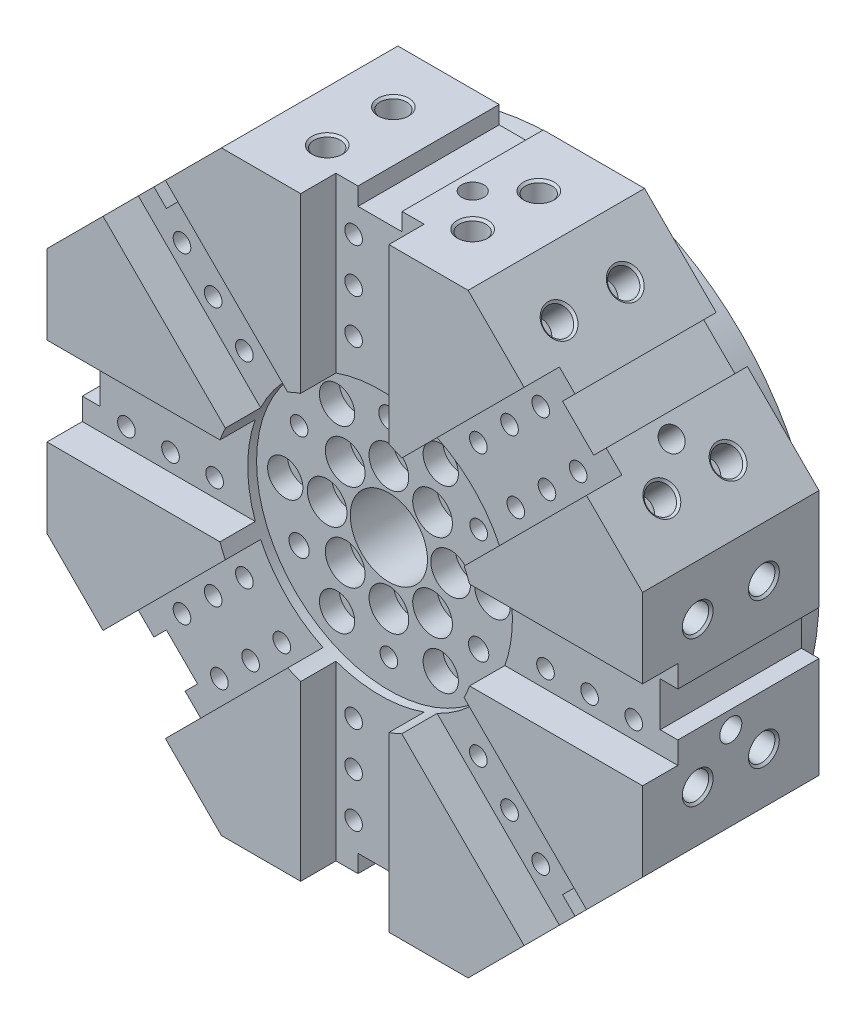
SolidWorks part; units mm, degrees
ref_plane "前视基准面" through (0, 0, 0) normal (0, 0, 1) x (1, 0, 0)
ref_plane "上视基准面" through (0, 0, 0) normal (0, 1, 0) x (1, 0, 0)
ref_plane "右视基准面" through (0, 0, 0) normal (1, 0, 0) x (0, 0, -1)
sketch "草图7" plane through (0, 0, 0) normal (0, 0, 1) x (1, 0, 0)
  line L1 (55.9188, 135) -> (-55.9188, 135)
  line L2 (-55.9188, 135) -> (-135, 55.9188)
  line L3 (-135, 55.9188) -> (-135, -55.9188)
  line L4 (-135, -55.9188) -> (-55.9188, -135)
  line L5 (-55.9188, -135) -> (55.9188, -135)
  line L6 (55.9188, -135) -> (135, -55.9188)
  line L7 (135, -55.9188) -> (135, 55.9188)
  line L8 (135, 55.9188) -> (55.9188, 135)
  circle A0 centre (0, 0) radius 135 construction
  dimension "D1" = 270
extrude "凸台-拉伸3" add sketch "草图7" along normal blind 80
sketch "草图8" plane through (0, 0, 80) normal (0, 0, 1) x (1, 0, 0)
  circle A0 centre (0, 0) radius 60
  dimension "D1" = 120
extrude "切除-拉伸3" cut sketch "草图8" against normal blind 20
sketch "草图9" plane through (0, 0, 80) normal (0, 0, 1) x (1, 0, 0)
  line L0 (0, 0) -> (228.1259, 0) construction
  line L1 (135, -55.9188) -> (135, 55.9188) construction
  line L2 (135, -20) -> (135, 20)
  line L3 (56.5685, -20) -> (135, -20)
  line L4 (56.5685, 20) -> (135, 20)
  line L5 (81.3173, -109.6016) -> (109.6016, -81.3173)
  line L6 (0, 20) -> (228.1259, 20) construction
  line L7 (0, -20) -> (228.1259, -20) construction
  line L8 (25.8579, -54.1421) -> (81.3173, -109.6016)
  line L9 (54.1421, -25.8579) -> (109.6016, -81.3173)
  line L10 (0, 0) -> (161.3093, -161.3093) construction
  line L11 (-20, -135) -> (20, -135)
  line L12 (-20, -56.5685) -> (-20, -135)
  line L13 (20, -56.5685) -> (20, -135)
  line L14 (0, 0) -> (0, -228.1259) construction
  line L15 (-109.6016, -81.3173) -> (-81.3173, -109.6016)
  line L16 (-54.1421, -25.8579) -> (-109.6016, -81.3173)
  line L17 (-25.8579, -54.1421) -> (-81.3173, -109.6016)
  line L18 (0, 0) -> (-161.3093, -161.3093) construction
  line L19 (-135, 20) -> (-135, -20)
  line L20 (-56.5685, 20) -> (-135, 20)
  line L21 (-56.5685, -20) -> (-135, -20)
  line L22 (0, 0) -> (-228.1259, 0) construction
  line L23 (-81.3173, 109.6016) -> (-109.6016, 81.3173)
  line L24 (-25.8579, 54.1421) -> (-81.3173, 109.6016)
  line L25 (-54.1421, 25.8579) -> (-109.6016, 81.3173)
  line L26 (0, 0) -> (-161.3093, 161.3093) construction
  line L27 (20, 135) -> (-20, 135)
  line L28 (20, 56.5685) -> (20, 135)
  line L29 (-20, 56.5685) -> (-20, 135)
  line L30 (0, 0) -> (0, 228.1259) construction
  line L31 (109.6016, 81.3173) -> (81.3173, 109.6016)
  line L32 (54.1421, 25.8579) -> (109.6016, 81.3173)
  line L33 (25.8579, 54.1421) -> (81.3173, 109.6016)
  line L34 (0, 0) -> (161.3093, 161.3093) construction
  circle A0 centre (0, 0) radius 60 construction
  arc A1 (56.5685, -20) -> (56.5685, 20) centre (0, 0) ccw
  arc A2 (25.8579, -54.1421) -> (54.1421, -25.8579) centre (0, 0) ccw
  arc A3 (-20, -56.5685) -> (20, -56.5685) centre (0, 0) ccw
  arc A4 (-54.1421, -25.8579) -> (-25.8579, -54.1421) centre (0, 0) ccw
  arc A5 (-56.5685, 20) -> (-56.5685, -20) centre (0, 0) ccw
  arc A6 (-25.8579, 54.1421) -> (-54.1421, 25.8579) centre (0, 0) ccw
  arc A7 (20, 56.5685) -> (-20, 56.5685) centre (0, 0) ccw
  arc A8 (54.1421, 25.8579) -> (25.8579, 54.1421) centre (0, 0) ccw
  dimension "D1" = 20
  dimension "D2" = 20
extrude "切除-拉伸4" cut sketch "草图9" against normal blind 16
sketch "草图10" plane through (0, 0, 64) normal (0, 0, 1) x (1, 0, 0)
  line L0 (0, 0) -> (184.1219, 0) construction
  line L1 (135, -20) -> (135, 20) construction
  line L2 (135, 10) -> (127, 10)
  line L3 (135, 10) -> (135, -10)
  line L4 (135, -10) -> (127, -10)
  line L5 (127, 10) -> (127, -10)
  dimension "D1" = 20
  dimension "D2" = 10
  dimension "D3" = 8
extrude "切除-拉伸5" cut sketch "草图10" against normal blind 146
pattern_circular "阵列(圆周)2" count 8 over 360 about axis through (0, 0, 0) along (0, 0, 1) of "切除-拉伸5"
sketch "草图11" plane through (0, 0, 64) normal (0, 0, 1) x (1, 0, 0)
  line L0 (0, 0) -> (174.2789, 0) construction
  line L1 (0, -12) -> (174.2789, -12) construction
  line L2 (0, 12) -> (174.2789, 12) construction
  line L4 (95, -12) -> (95, 12) construction
  line L5 (115, 20) -> (115, 55.9188)
  line L6 (115, -12) -> (115, 12) construction
  line L7 (75, -12) -> (75, 12) construction
  line L8 (115, 20) -> (115, 55.9188) construction
  line L9 (95, 20) -> (95, 55.9188) construction
  line L10 (75, 20) -> (75, 55.9188) construction
  circle A0 centre (115, 12) radius 4
  circle A1 centre (95, 12) radius 4
  circle A2 centre (75, 12) radius 4
  circle A3 centre (75, -12) radius 4
  circle A4 centre (95, -12) radius 4
  circle A5 centre (115, -12) radius 4
  dimension "D6" = 8
  dimension "D7" = 8
  dimension "D8" = 8
  dimension "D9" = 8
  dimension "D10" = 8
  dimension "D11" = 8
  dimension "D1" = 12
  dimension "D2" = 12
  dimension "D3" = 20
  dimension "D4" = 20
  dimension "D5" = 20
extrude "切除-拉伸6" cut sketch "草图11" against normal blind 15
pattern_circular "阵列(圆周)3" count 8 over 360 about axis through (0, 0, 0) along (0, 0, 1) of "切除-拉伸6"
sketch "草图12" plane through (135, 0, 0) normal (1, 0, 0) x (0, 0, -1)
  line L0 (0, 32.9594) -> (-106.8945, 32.9594) construction
  line L1 (0, 10) -> (0, 55.9188) construction
  line L2 (-80, 20) -> (-80, 55.9188) construction
  circle A0 centre (-25, 32.9594) radius 6
  circle A1 centre (-55, 32.9594) radius 6
  dimension "D1" = 12
  dimension "D2" = 12
  dimension "D3" = 25
  dimension "D4" = 25
extrude "切除-拉伸7" cut sketch "草图12" against normal blind 15
chamfer "倒角1" distance 1 angle 45 2 edges at (135, 32.9594, 49) (135, 32.9594, 19)
mirror "镜向1" about plane through (0, 0, 0) normal (0, 1, 0) of "切除-拉伸7"
chamfer "倒角2" distance 1 angle 45 3 edges at (135, -32.9594, 49) (120, -32.9594, 49) (135, -32.9594, 19)
pattern_circular "阵列(圆周)6" count 8 over 360 about axis through (0, 0, 0) along (0, 0, 1) of "切除-拉伸7", "镜向1"
chamfer "倒角3" distance 1 angle 45 28 edges at (118.7652, -72.1536, 49) (118.7652, -72.1536, 19) (72.1536, -118.7652, 19) (72.1536, -118.7652, 49) (32.9594, -135, 49) (32.9594, -135, 19) (-32.9594, -135, 49) (-32.9594, -135, 19) (-72.1536, -118.7652, 19) (-72.1536, -118.7652, 49) (-118.7652, -72.1536, 49) (-118.7652, -72.1536, 19) (-135, -32.9594, 49) (-135, -32.9594, 19) (-135, 32.9594, 19) (-135, 32.9594, 49) (-118.7652, 72.1536, 49) (-118.7652, 72.1536, 19) (-72.1536, 118.7652, 49) (-72.1536, 118.7652, 19) (-32.9594, 135, 19) (-32.9594, 135, 49) (32.9594, 135, 49) (32.9594, 135, 19) (72.1536, 118.7652, 49) (72.1536, 118.7652, 19) (118.7652, 72.1536, 49) (118.7652, 72.1536, 19)
sketch "草图13" plane through (0, 0, 0) normal (0, 0, -1) x (-1, 0, 0)
  circle A0 centre (0, 0) radius 120
  dimension "D1" = 240
extrude "凸台-拉伸4" add sketch "草图13" along normal blind 15
sketch "草图14" plane through (0, 0, 60) normal (0, 0, 1) x (1, 0, 0)
  circle A0 centre (28, 0) radius 5
  circle A1 centre (47, 0) radius 4
  circle A2 centre (19.799, -19.799) radius 5
  circle A3 centre (0, -28) radius 5
  circle A4 centre (-19.799, -19.799) radius 5
  circle A5 centre (-28, 0) radius 5
  circle A6 centre (-19.799, 19.799) radius 5
  circle A7 centre (0, 28) radius 5
  circle A8 centre (19.799, 19.799) radius 5
  circle A9 centre (23.5, -40.7032) radius 4
  circle A10 centre (-23.5, -40.7032) radius 4
  circle A11 centre (-47, 0) radius 4
  circle A12 centre (-23.5, 40.7032) radius 4
  circle A13 centre (23.5, 40.7032) radius 4
  dimension "D1" = 10
  dimension "D2" = 8
  dimension "D4" = 19
  dimension "D3" = 28
extrude "切除-拉伸8" cut sketch "草图14" against normal blind 35
sketch "草图15" plane through (0, 0, 60) normal (0, 0, 1) x (1, 0, 0)
  circle A0 centre (0, 0) radius 17.5
  dimension "D1" = 35
extrude "切除-拉伸9" cut sketch "草图15" against normal blind 85
sketch "草图16" plane through (0, 0, 60) normal (0, 0, 1) x (1, 0, 0)
  circle A121 centre (47, 0) radius 8
  circle A122 centre (47, 0) radius 8
  circle A124 centre (23.5, -40.7032) radius 8
  circle A125 centre (-23.5, -40.7032) radius 8
  circle A127 centre (-47, 0) radius 8
  circle A128 centre (-23.5, 40.7032) radius 8
  circle A130 centre (23.5, 40.7032) radius 8
  circle A131 centre (47, 0) radius 4 construction
  circle A133 centre (23.5, 40.7032) radius 4 construction
  dimension "D1" = 4
  dimension "D2" = 6
extrude "切除-拉伸10" cut sketch "草图16" against normal blind 9
sketch "草图17" plane through (0, 0, 60) normal (0, 0, 1) x (1, 0, 0)
  circle A2 centre (28, 0) radius 9
  circle A3 centre (19.799, 19.799) radius 9
  circle A4 centre (19.799, 19.799) radius 9
  circle A5 centre (19.799, -19.799) radius 9
  circle A6 centre (0, -28) radius 9
  circle A7 centre (-19.799, -19.799) radius 9
  circle A8 centre (-28, 0) radius 9
  circle A9 centre (-19.799, 19.799) radius 9
  circle A10 centre (0, 28) radius 9
  circle A11 centre (19.799, 19.799) radius 5 construction
  circle A12 centre (28, 0) radius 5 construction
  dimension "D1" = 4
  dimension "D2" = 8
extrude "切除-拉伸11" cut sketch "草图17" against normal blind 11
sketch "草图18" plane through (0, 0, 60) normal (0, 0, 1) x (1, 0, 0)
  circle A0 centre (0, 0) radius 47 construction
  circle A1 centre (0, -47) radius 4
  dimension "D1" = 8
  dimension "D2" = 94
extrude "切除-拉伸12" cut sketch "草图18" against normal blind 8
pattern_circular "阵列(圆周)7" count 3 over 360 about axis through (0, 0, 0) along (0, 0, 1) of "切除-拉伸12"
sketch "草图19" plane through (0, 0, -15) normal (0, 0, -1) x (-1, 0, 0)
  circle A0 centre (0, 0) radius 85
  dimension "D1" = 170
extrude "切除-拉伸13" cut sketch "草图19" against normal blind 40
sketch "草图20" plane through (0, 0, 60) normal (0, 0, 1) x (1, 0, 0)
  line L0 (40.7032, -23.5) -> (0, 0) construction
  line L1 (0, 0) -> (77.7876, 0) construction
  circle A0 centre (0, 0) radius 47 construction
  circle A1 centre (40.7032, -23.5) radius 4.6
  circle A2 centre (-40.7032, -23.5) radius 4.6
  circle A3 centre (0, 47) radius 4.6
  dimension "D1" = 9.2
  dimension "D2" = 30
  dimension "D3" = 3
extrude "切除-拉伸14" cut sketch "草图20" against normal blind 143
sketch "草图21" plane through (95.4594, 95.4594, 0) normal (0.7071, 0.7071, 0) x (0, 0, -1)
  line L0 (0, -10) -> (-64, -10) construction
  line L1 (-80, -55.9188) -> (-80, -20) construction
  circle A0 centre (-40, -18) radius 5
  dimension "D1" = 10
  dimension "D2" = 8
  dimension "D3" = 40
extrude "切除-拉伸15" cut sketch "草图21" against normal blind 50
pattern_circular "阵列(圆周)8" count 8 over 360 about axis through (0, 0, 0) along (0, 0, 1) of "切除-拉伸15"
sketch "草图22" plane through (0, 0, -15) normal (0, 0, -1) x (-1, 0, 0)
  circle A0 centre (-98.2596, -18.0047) radius 5
  circle A3 centre (-98.2596, -18.0047) radius 5 construction
  dimension "D1" = 10
extrude "切除-拉伸16" cut sketch "草图22" against normal blind 65
ref_plane "基准面2" through (0, -18.0047, 0) normal (0, 1, 0) x (-1, 0, 0)
pattern_circular "阵列(圆周)9" count 8 over 360 about axis through (0, 0, 0) along (0, 0, 1) of "切除-拉伸16"
